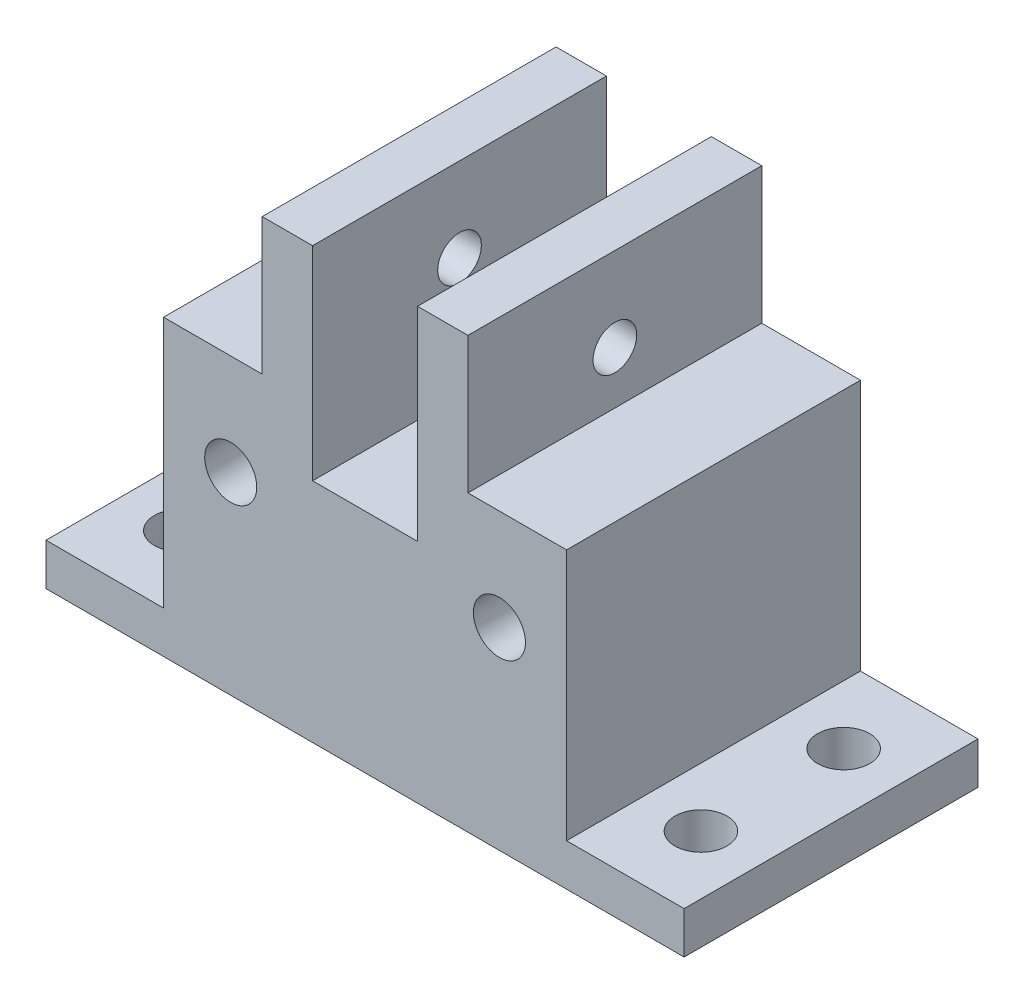
SolidWorks part; units mm, degrees
ref_plane "Front Plane" through (0, 0, 0) normal (0, 0, 1) x (1, 0, 0)
ref_plane "Top Plane" through (0, 0, 0) normal (0, 1, 0) x (1, 0, 0)
ref_plane "Right Plane" through (0, 0, 0) normal (1, 0, 0) x (0, 0, -1)
sketch "Sketch1" plane through (0, 0, 0) normal (0, 0, 1) x (1, 0, 0)
  line L1 (-5, -3.75) -> (-35, -3.75)
  line L2 (-35, -3.75) -> (-35, -28.75)
  line L3 (-35, -28.75) -> (13, -28.75)
  line L6 (-5, -3.75) -> (13, -3.75)
  line L7 (5, -15.75) -> (13, -15.75) construction
  line L8 (13, -28.75) -> (13, -3.75)
  circle A0 centre (5, -15.75) radius 3.1
  circle A1 centre (-27, -15.75) radius 3.1
  dimension "D5" = 6.2
  dimension "D6" = 6.2
  dimension "D1" = 8
  dimension "D2" = 8
  dimension "D3" = 32
  dimension "D4" = 12
extrude "Boss-Extrude1" add sketch "Sketch1" along normal blind 35
sketch "Sketch2" plane through (0, 0, 0) normal (0, 0, -1) x (-1, 0, 0)
  circle A0 centre (27, -15.75) radius 3.1 construction
  circle A1 centre (-5, -15.75) radius 3.1 construction
  circle A2 centre (27, -15.75) radius 3.1
  circle A3 centre (-5, -15.75) radius 3.1
extrude "Boss-Extrude2" add sketch "Sketch2" against normal blind 5
sketch "Sketch3" plane through (0, 0, 35) normal (0, 0, 1) x (1, 0, 0)
  line L0 (-11, -28.75) -> (-11, 2.5) construction
  line L1 (-35, -28.75) -> (13, -28.75) construction
  line L2 (-17.25, 2.5) -> (-4.75, 2.5) construction
  line L3 (-17.25, 2.5) -> (-17.25, -7.5)
  line L4 (-17.25, 2.5) -> (-17.25, 12.5)
  line L5 (-4.75, 2.5) -> (-4.75, -7.5)
  line L6 (-4.75, 2.5) -> (-4.75, 12.5)
  line L7 (-17.25, 12.5) -> (-23.25, 12.5)
  line L8 (-23.25, 12.5) -> (-23.25, -7.5)
  line L9 (-23.25, -7.5) -> (-17.25, -7.5)
  line L10 (1.25, -7.5) -> (-4.75, -7.5)
  line L11 (1.25, 12.5) -> (1.25, -7.5)
  line L12 (-4.75, 12.5) -> (1.25, 12.5)
  point P6 (-11, 2.5)
  dimension "D1" = 31.25
  dimension "D2" = 12.5
  dimension "D3" = 10
  dimension "D4" = 10
  dimension "D5" = 6
extrude "Boss-Extrude3" add sketch "Sketch3" against normal up to surface (35 mm away) up to face at (-11, -16.25, 0)
sketch "Sketch4" plane through (-23.25, 0, 0) normal (-1, 0, 0) x (0, 0, 1)
  line L0 (35, -7.5) -> (0, -7.5) construction
  line L1 (35, 12.5) -> (35, -7.5) construction
  line L2 (35, -28.75) -> (35, 2.5) construction
  line L3 (0, -3.75) -> (0, -28.75) construction
  line L4 (17.5, -7.5) -> (17.5, 2.5) construction
  circle A0 centre (17.5, 2.5) radius 2.6
  dimension "D2" = 5.2
  dimension "D1" = 10
extrude "Cut-Extrude1" cut sketch "Sketch4" against normal through all
sketch "Sketch6" plane through (0, 0, 35) normal (0, 0, 1) x (1, 0, 0)
  line L0 (-17.25, -3.75) -> (-17.25, -11.75)
  line L1 (-17.25, -11.75) -> (-4.75, -11.75)
  line L2 (-4.75, -11.75) -> (-4.75, -3.75)
  line L3 (-17.25, -3.75) -> (-4.75, -3.75)
extrude "Cut-Extrude2" cut sketch "Sketch6" against normal through all
sketch "Sketch7" plane through (0, -28.75, 0) normal (0, -1, 0) x (1, 0, 0)
  line L4 (-35, 0) -> (13, 0)
  line L5 (13, 0) -> (13, 35)
  line L6 (13, 35) -> (-35, 35)
  line L7 (-35, 35) -> (-35, 0)
  line L8 (-35, 0) -> (13, 0)
  line L9 (13, 0) -> (13, 35)
  line L10 (13, 35) -> (-35, 35)
  line L11 (-35, 35) -> (-35, 0)
  dimension "D1" = 0
extrude "Boss-Extrude4" add sketch "Sketch7" along normal blind 10
sketch "Sketch8" plane through (0, -38.75, 0) normal (0, -1, 0) x (1, 0, 0)
  line L0 (-35, 35) -> (-49, 35)
  line L1 (-49, 35) -> (-49, 0)
  line L2 (-49, 0) -> (-35, 0)
  line L3 (-11, 35) -> (-11, -5.7205) construction
  line L4 (13, 35) -> (-35, 35) construction
  line L5 (-35, 35) -> (-35, 0)
  line L7 (27, 0) -> (13, 0)
  line L8 (27, 35) -> (27, 0)
  line L9 (13, 35) -> (27, 35)
  line L10 (13, 35) -> (13, 0)
  circle A0 centre (-42, 9) radius 3.1
  circle A1 centre (20, 9) radius 3.1
  circle A2 centre (-42, 26) radius 3.1
  circle A3 centre (20, 26) radius 3.1
  dimension "D1" = 6.2
  dimension "6.2" = 6.2
  dimension "D3" = 6.2
  dimension "D4" = 9
  dimension "D6" = 9
  dimension "D7" = 9
  dimension "D5" = 9
extrude "Boss-Extrude5" add sketch "Sketch8" against normal blind 5
